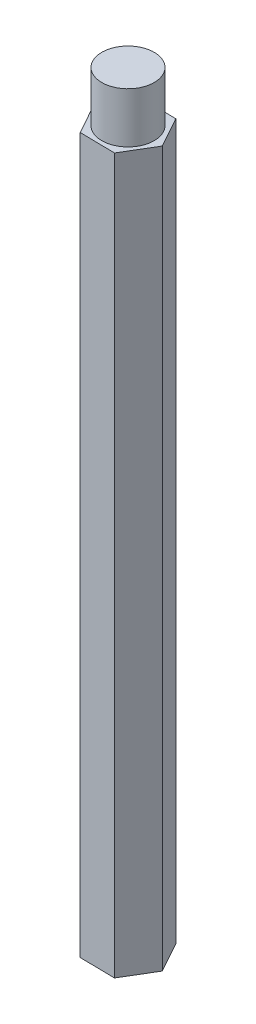
SolidWorks part; units mm, degrees
material "Brass"
ref_plane "Front Plane" through (0, 0, 0) normal (0, 0, 1) x (1, 0, 0)
ref_plane "Top Plane" through (0, 0, 0) normal (0, 1, 0) x (1, 0, 0)
ref_plane "Right Plane" through (0, 0, 0) normal (1, 0, 0) x (0, 0, -1)
sketch "Sketch1" plane through (0, 0, 0) normal (0, 1, 0) x (1, 0, 0)
  line L1 (1.067, -1.917) -> (2.1937, -0.0345)
  line L2 (2.1937, -0.0345) -> (1.1267, 1.8825)
  line L3 (1.1267, 1.8825) -> (-1.067, 1.917)
  line L4 (-1.067, 1.917) -> (-2.1937, 0.0345)
  line L5 (-2.1937, 0.0345) -> (-1.1267, -1.8825)
  line L6 (-1.1267, -1.8825) -> (1.067, -1.917)
  circle A0 centre (0, 0) radius 1.9 construction
  dimension "D1" = 1.9
extrude "Boss-Extrude1" add sketch "Sketch1" along normal blind 45
sketch "Sketch2" plane through (0, 45, 0) normal (0, 1, 0) x (1, 0, 0)
  circle A0 centre (0, 0) radius 1.65
  dimension "D1" = 3.3
extrude "Boss-Extrude2" add sketch "Sketch2" along normal blind 3.175
